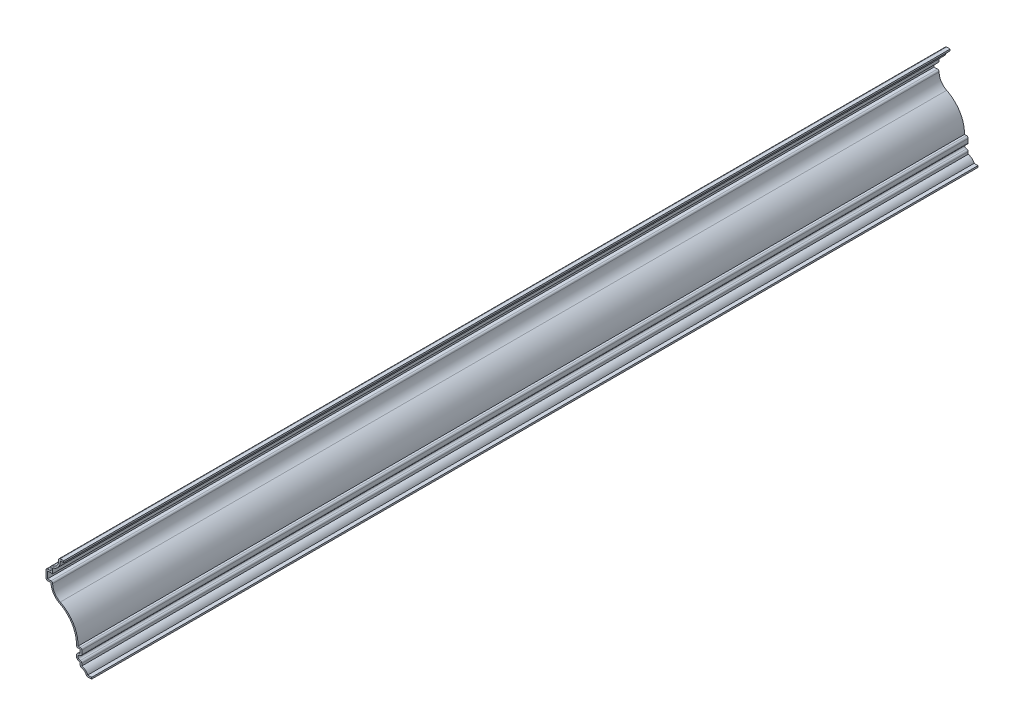
SolidWorks part; units mm, degrees
ref_plane "Front Plane" through (0, 0, 0) normal (0, 0, 1) x (1, 0, 0)
ref_plane "Top Plane" through (0, 0, 0) normal (0, 1, 0) x (1, 0, 0)
ref_plane "Right Plane" through (0, 0, 0) normal (1, 0, 0) x (0, 0, -1)
sketch "Sketch1" plane through (0, 0, 0) normal (0, 0, 1) x (1, 0, 0)
  line L0 (0, 0) -> (-3.175, 0)
  line L1 (-7.1437, 3.175) -> (-7.1437, 5.5563)
  line L2 (-7.1437, 10.3187) -> (-7.1438, 12.7)
  line L3 (-7.1438, 12.7) -> (-9.525, 12.7)
  line L4 (-25.4, 39.6875) -> (-28.575, 39.6875)
  line L5 (-28.575, 39.6875) -> (-28.575, 46.0375)
  line L6 (-28.575, 46.0375) -> (-25.4, 46.0375)
  line L7 (-25.4, 46.0375) -> (-25.4, 49.2125)
  line L8 (-20.6375, 53.975) -> (-20.6375, 55.5625)
  line L9 (-20.6375, 55.5625) -> (-17.4625, 55.5625)
  line L10 (-9.525, 12.7) -> (-9.525, 6.5097) construction
  arc A0 (-3.175, 0) -> (-7.1437, 3.175) centre (-7.1437, -0.893) ccw
  arc A1 (-7.1437, 5.5563) -> (-7.1437, 10.3187) centre (-7.1437, 7.9375) cw
  arc A2 (-9.525, 12.7) -> (-20.092, 31.1469) centre (-28.526, 14.0656) ccw
  arc A3 (-20.092, 31.1469) -> (-25.4, 39.6875) centre (-15.875, 39.6875) cw
  arc A4 (-25.4, 49.2125) -> (-20.6375, 53.975) centre (-25.4, 53.975) ccw
  point P2 (-45.6584, -0.0878)
  point P20 (-101.256, 25.221)
  point P27 (0, 0)
  dimension "D7" = 2.3813
  dimension "D10" = 3.175
  dimension "D11" = 6.35
  dimension "D16" = 3.175
  dimension "D4" = 2.3813
  dimension "D8" = 19.05
  dimension "D9" = 9.525
  dimension "D15" = 4.7625
  dimension "D1" = 3.175
  dimension "D2" = 3.9688
  dimension "D3" = 2.3813
  dimension "D5" = 2.3813
  dimension "D6" = 3.175
  dimension "D12" = 3.175
  dimension "D13" = 26.9875
  dimension "D14" = 6.35
  dimension "D17" = 3.175
  dimension "D18" = 4.7625
  dimension "D19" = 28.575
  dimension "D21" = 11.1125
extrude "Extrude-Thin1" add sketch "Sketch1" against normal blind 555.625 thin
fillet "Fillet1" radius 1.016 11 edges at (-3.175, 0, -277.8125) (-7.1437, 3.175, -277.8125) (-6.1277, 7.0256, -277.8125) (-6.1277, 8.8494, -277.8125) (-6.1278, 13.716, -277.8125) (-9.525, 12.7, -277.8125) (-24.3231, 40.7035, -277.8125) (-28.575, 39.6875, -277.8125) (-28.575, 46.0375, -277.8125) (-25.4, 49.2125, -277.8125) (-20.6375, 55.5625, -277.8125)
